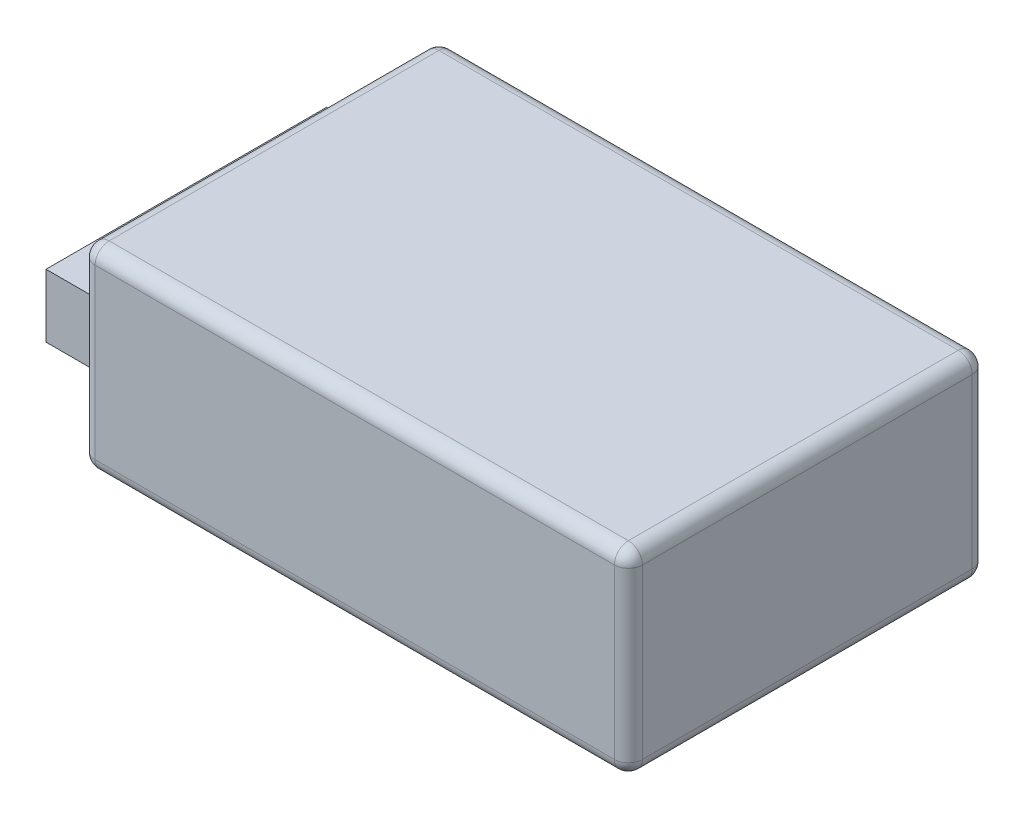
SolidWorks part; units mm, degrees
ref_plane "Front Plane" through (0, 0, 0) normal (0, 0, 1) x (1, 0, 0)
ref_plane "Top Plane" through (0, 0, 0) normal (0, 1, 0) x (1, 0, 0)
ref_plane "Right Plane" through (0, 0, 0) normal (1, 0, 0) x (0, 0, -1)
sketch "Sketch2" plane through (0, 0, 0) normal (0, 1, 0) x (1, 0, 0)
  line L1 (-39, -25.5) -> (39, -25.5)
  line L2 (-39, -25.5) -> (-39, 25.5)
  line L3 (-39, 25.5) -> (39, 25.5)
  line L4 (39, -25.5) -> (39, 25.5)
  line L5 (-39, -25.5) -> (39, 25.5) construction
  line L6 (-39, 25.5) -> (39, -25.5) construction
  point P0 (0, 0)
  dimension "D1" = 78
  dimension "D2" = 51
extrude "Boss-Extrude1" add sketch "Sketch2" along normal blind 28
sketch "Sketch3" plane through (-39, 0, 0) normal (-1, 0, 0) x (0, 0, 1)
  line L0 (-25.5, 28) -> (-25.5, 0) construction
  line L1 (-23.5, 4) -> (16.5, 4)
  line L2 (-23.5, 4) -> (-23.5, 13)
  line L3 (-23.5, 13) -> (16.5, 13)
  line L4 (16.5, 4) -> (16.5, 13)
  line L5 (-23.5, 4) -> (16.5, 13) construction
  line L6 (-23.5, 13) -> (16.5, 4) construction
  line L7 (-25.5, 0) -> (25.5, 0) construction
  point P0 (-3.5, 8.5)
  dimension "D1" = 40
  dimension "D2" = 9
  dimension "D3" = 2
  dimension "D4" = 4
extrude "Boss-Extrude2" add sketch "Sketch3" along normal blind 14 separate body
fillet "Fillet1" radius 2 12 edges at (-39, 14, -25.5) (-39, 14, 25.5) (39, 14, 25.5) (39, 14, -25.5) (0, 0, -25.5) (-39, 0, 0) (0, 0, 25.5) (39, 0, 0) (0, 28, 25.5) (-39, 28, 0) (0, 28, -25.5) (39, 28, 0)
